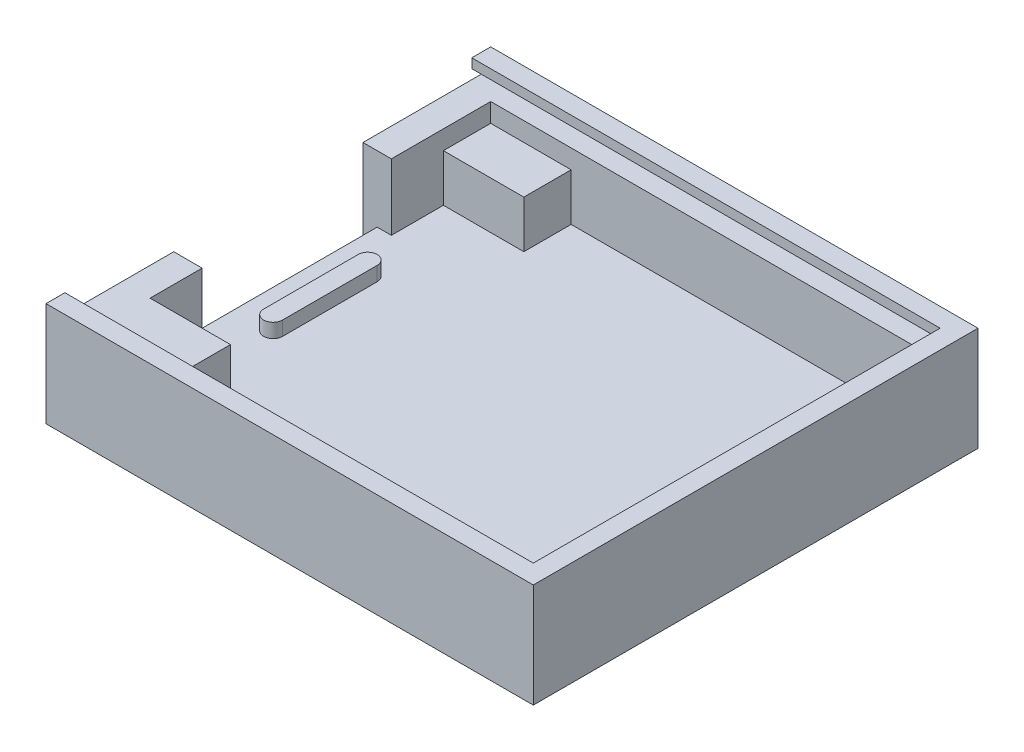
SolidWorks part; units mm, degrees
ref_plane "Alzado" through (0, 0, 0) normal (0, 0, 1) x (1, 0, 0)
ref_plane "Planta" through (0, 0, 0) normal (0, 1, 0) x (1, 0, 0)
ref_plane "Vista lateral" through (0, 0, 0) normal (1, 0, 0) x (0, 0, -1)
sketch "Croquis1" plane through (0, 0, 0) normal (0, 1, 0) x (1, 0, 0)
  line L1 (-51.5, 47) -> (0, 47)
  line L2 (-51.5, 47) -> (-51.5, 0)
  line L3 (-51.5, 0) -> (0, 0)
  line L4 (0, 47) -> (0, 0)
  line L5 (-51.5, 47) -> (0, 0) construction
  line L6 (-51.5, 0) -> (0, 47) construction
  point P0 (-25.75, 23.5)
  dimension "D1" = 51.5
  dimension "D2" = 47
extrude "Saliente-Extruir1" add sketch "Croquis1" along normal blind 2
sketch "Croquis2" plane through (0, 2, 0) normal (0, 1, 0) x (1, 0, 0)
  line L0 (-51.5, 0) -> (0, 0) construction
  line L1 (-51.5, 47) -> (-51.5, 0) construction
  line L2 (-51.5, 47) -> (-51.5, 0)
  line L3 (-51.5, 47) -> (-50, 47)
  line L4 (-51.5, 47) -> (-51.5, 0)
  line L5 (-51.5, 0) -> (-50, 0)
  line L6 (-50, 47) -> (-50, 0)
  line L7 (-46, 28.5) -> (-46, 18.5) construction
  line L9 (-50, 47) -> (-50, 0)
  line L12 (-45, 28.5) -> (-45, 18.5)
  line L13 (-47, 28.5) -> (-47, 18.5)
  arc A0 (-45, 28.5) -> (-47, 28.5) centre (-46, 28.5) ccw
  arc A1 (-47, 18.5) -> (-45, 18.5) centre (-46, 18.5) ccw
  point P9 (-50, 23.5)
  point P13 (-46, 23.5)
  dimension "D1" = 1.5
  dimension "D2" = 5.5
  dimension "D3" = 2
  dimension "D4" = 12
extrude "Saliente-Extruir11" add sketch "Croquis2" along normal blind 1.5 contours L12 A1 L13 A0
sketch "Croquis3" plane through (0, 2, 0) normal (0, 1, 0) x (1, 0, 0)
  line L4 (-51.5, 47) -> (-51.5, 0) construction
  line L5 (0, 47) -> (-51.5, 47) construction
  line L6 (0, 0) -> (0, 47) construction
  line L7 (-51.5, 0) -> (0, 0) construction
  line L8 (-51.5, 47) -> (-51.5, 0)
  line L9 (0, 47) -> (-51.5, 47)
  line L10 (0, 0) -> (0, 47)
  line L11 (-51.5, 0) -> (0, 0)
  line L12 (-48.5, 44) -> (-48.5, 3)
  line L13 (-48.5, 3) -> (-3, 3)
  line L14 (-3, 3) -> (-3, 44)
  line L15 (-3, 44) -> (-48.5, 44)
  dimension "D1" = 3
extrude "Saliente-Extruir10" add sketch "Croquis3" along normal blind 7
sketch "Croquis4" plane through (0, 9, 0) normal (0, 1, 0) x (1, 0, 0)
  line L0 (-48.5, 44) -> (-48.5, 3) construction
  line L2 (-51.5, 33.5) -> (-48.5, 33.5)
  line L3 (-51.5, 33.5) -> (-51.5, 13.5)
  line L4 (-51.5, 13.5) -> (-48.5, 13.5)
  line L5 (-48.5, 33.5) -> (-48.5, 13.5)
  line L6 (-51.5, 47) -> (-51.5, 0) construction
  line L7 (-51.5, 47) -> (-51.5, 0)
  point P0 (-48.5, 23.5)
  point P7 (-48.5, 23.5)
  line M2 (-51.5, 47) -> (-51.5, 0)
  line M5 (-48.5, 3) -> (-48.5, 44)
  dimension "D2" = 20
extrude "Cortar-Extruir3" cut sketch "Croquis4" against normal blind 7 contours L4 L2 M2 M5
sketch "Croquis5" plane through (0, 2, 0) normal (0, 1, 0) x (1, 0, 0)
  line L0 (-51.5, 13.5) -> (-51.5, 0) construction
  line L1 (-48.5, 3) -> (-40, 3)
  line L2 (-48.5, 3) -> (-48.5, 8)
  line L3 (-48.5, 8) -> (-40, 8)
  line L4 (-40, 3) -> (-40, 8)
  dimension "D1" = 5
  dimension "D2" = 11.5
extrude "Saliente-Extruir12" add sketch "Croquis5" along normal blind 7
sketch "Croquis6" plane through (-40, 0, 0) normal (1, 0, 0) x (0, 0, -1)
  line L0 (8, 9) -> (8, 2) construction
  line L1 (3, 9) -> (8, 9) construction
  circle A0 centre (5.5, 5.5) radius 0.5
  point P0 (5.5, 5.5)
  point P3 (8, 5.5)
  point P4 (5.5, 9)
  dimension "D1" = 1
extrude "Cortar-Extruir2" cut sketch "Croquis6" against normal through all
sketch "Croquis8" plane through (0, 2, 0) normal (0, 1, 0) x (1, 0, 0)
  line L0 (-51.5, 47) -> (-51.5, 33.5) construction
  line L1 (-48.5, 44) -> (-40, 44)
  line L2 (-48.5, 44) -> (-48.5, 39)
  line L3 (-48.5, 39) -> (-40, 39)
  line L4 (-40, 44) -> (-40, 39)
  dimension "D1" = 5
  dimension "D2" = 11.5
extrude "Saliente-Extruir13" add sketch "Croquis8" along normal blind 5
sketch "Croquis9" plane through (0, 9, 0) normal (0, 1, 0) x (1, 0, 0)
  line L0 (-51.5, 1) -> (-1, 1)
  line L1 (-51.5, 13.5) -> (-51.5, 0) construction
  line L2 (-1, 1) -> (-1, 46)
  line L3 (-1, 46) -> (-51.5, 46)
  line L4 (-51.5, 47) -> (-51.5, 33.5) construction
  line L5 (-51.5, 46) -> (-51.5, 47)
  line L6 (-51.5, 47) -> (0, 47)
  line L7 (0, 47) -> (0, 0)
  line L8 (0, 0) -> (-51.5, 0)
  line L9 (-51.5, 0) -> (-51.5, 1)
  dimension "D1" = 1
  dimension "D2" = 1
  dimension "D3" = 1
extrude "Saliente-Extruir14" add sketch "Croquis9" along normal blind 2
sketch "Croquis10" plane through (0, 0, -46) normal (0, 0, 1) x (1, 0, 0)
  line L0 (-1, 11) -> (-1, 9) construction
  line L1 (-51.5, 11) -> (-1, 11)
  line L2 (-51.5, 11) -> (-51.5, 10)
  line L3 (-51.5, 10) -> (-1, 10)
  line L4 (-1, 11) -> (-1, 10)
extrude "Saliente-Extruir15" add sketch "Croquis10" along normal blind 1
sketch "Croquis11" plane through (0, 0, -1) normal (0, 0, -1) x (-1, 0, 0)
  line L0 (1, 11) -> (1, 9) construction
  line L1 (51.5, 11) -> (1, 11)
  line L2 (51.5, 11) -> (51.5, 10)
  line L3 (51.5, 10) -> (1, 10)
  line L4 (1, 11) -> (1, 10)
extrude "Saliente-Extruir16" add sketch "Croquis11" along normal blind 1
sketch "Croquis12" plane through (-1, 0, 0) normal (-1, 0, 0) x (0, 0, 1)
  line L1 (-2, 11) -> (-45, 11)
  line L2 (-2, 11) -> (-2, 10)
  line L3 (-2, 10) -> (-45, 10)
  line L4 (-45, 11) -> (-45, 10)
extrude "Saliente-Extruir17" add sketch "Croquis12" along normal blind 1
sketch "Croquis13" plane through (0, 2, 0) normal (0, 1, 0) x (1, 0, 0)
  line L0 (-51.5, 33.5) -> (-48.5, 33.5) construction
  line L1 (-51.5, 13.5) -> (-50, 13.5)
  line L2 (-51.5, 13.5) -> (-51.5, 33.5)
  line L3 (-51.5, 33.5) -> (-50, 33.5)
  line L4 (-50, 13.5) -> (-50, 33.5)
extrude "Cortar-Extruir4" cut sketch "Croquis13" against normal through all
